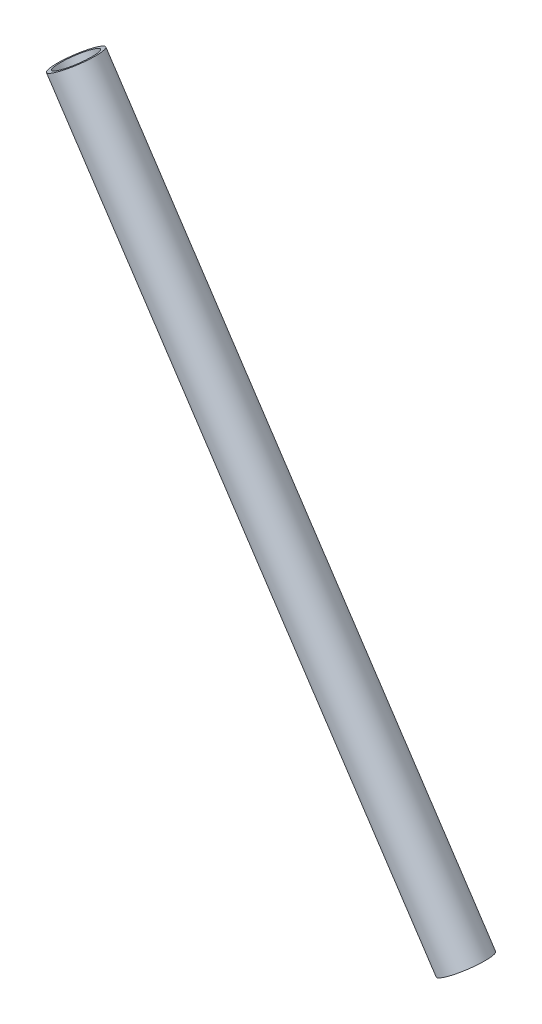
SolidWorks part; units mm, degrees
ref_plane "Front" through (0, 0, 0) normal (0, 0, 1) x (1, 0, 0)
ref_plane "Top" through (0, 0, 0) normal (0, 1, 0) x (1, 0, 0)
ref_plane "Right" through (0, 0, 0) normal (1, 0, 0) x (0, 0, -1)
sketch "Sketch1" plane through (0, 0, 0) normal (0, 0, 1) x (1, 0, 0)
  line L0 (317.4842, 618.251) -> (479.6942, 373.3508) construction
  line L1 (506.8697, 332.322) -> (290.3087, 659.2798) construction
  line L2 (479.6942, 373.3508) -> (473.1296, 369.0027) construction
  line L3 (473.1296, 369.0027) -> (471.7531, 368.091)
  line L4 (471.7531, 368.091) -> (309.5431, 612.9912)
  line L5 (309.5431, 612.9912) -> (310.9196, 613.9029)
  line L6 (310.9196, 613.9029) -> (473.1296, 369.0027)
  line L7 (310.9196, 613.9029) -> (317.4842, 618.251) construction
  dimension "D1" = 1.651
  dimension "D2" = 9.525
revolve "Revolve1" add sketch "Sketch1" angle 360 about L0
equation "\"D1@Sketch1\"=\"a arm tube thickness@FS2-SU-FS-A-0002-V1, FRONT LEFT SUSPENSION.SLDASM\""
equation "\"D2@Sketch1\"=\"a arm tube diameter@FS2-SU-FS-A-0002-V1, FRONT LEFT SUSPENSION.SLDASM\"/2"
